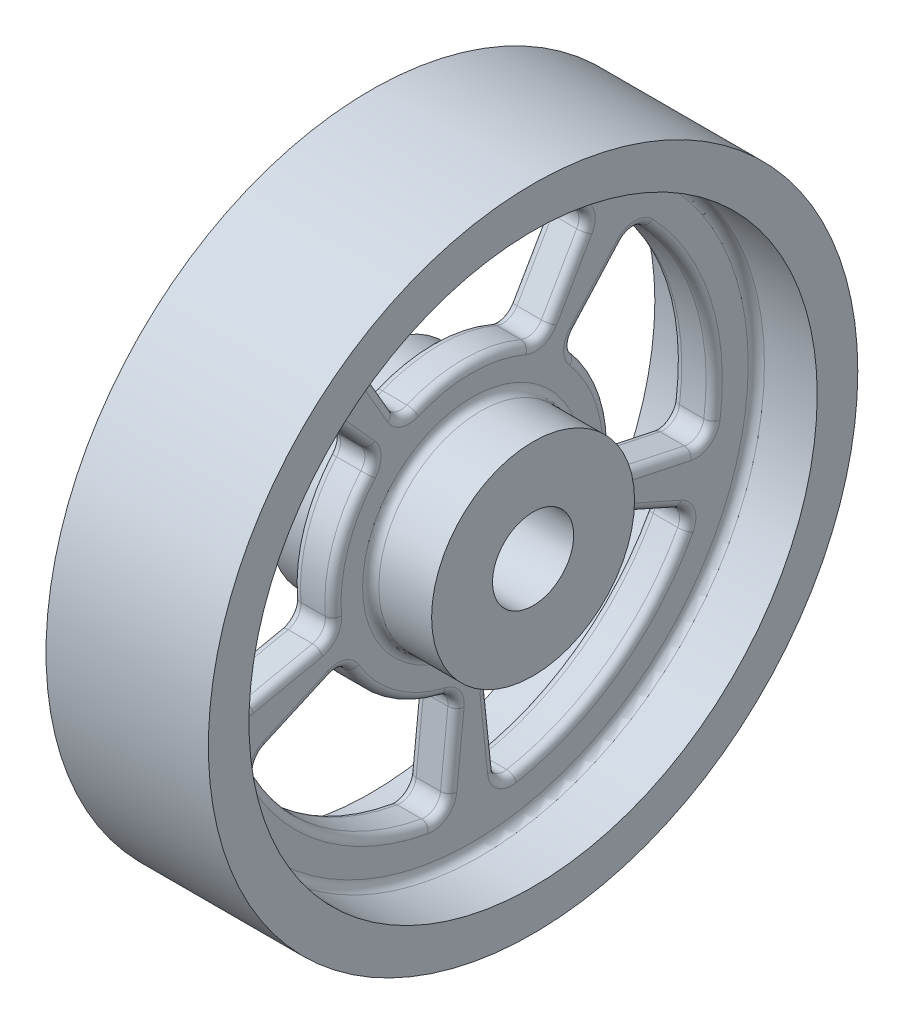
SolidWorks part; units mm, degrees
ref_plane "Front Plane" through (0, 0, 0) normal (0, 0, 1) x (1, 0, 0)
ref_plane "Top Plane" through (0, 0, 0) normal (0, 1, 0) x (1, 0, 0)
ref_plane "Right Plane" through (0, 0, 0) normal (1, 0, 0) x (0, 0, -1)
sketch "Sketch1" plane through (0, 0, 0) normal (0, 0, 1) x (1, 0, 0)
  line L0 (2.5, 12.5) -> (10, 12.5)
  line L9 (-10, 40) -> (10, 40)
  line L10 (-10, 40) -> (-10, 35)
  line L11 (-10, 35) -> (-2.5, 35)
  line L12 (10, 40) -> (10, 35)
  line L13 (0, 84.9625) -> (0, 0) construction
  line L14 (44.4387, 0) -> (0, 0) construction
  line L16 (-2.5, 35) -> (-2.5, 12.5)
  line L18 (2.5, 35) -> (2.5, 12.5)
  line L20 (10, 5) -> (-10, 5)
  line L21 (-10, 12.5) -> (-2.5, 12.5)
  line L22 (-10, 12.5) -> (-10, 5)
  line L24 (10, 12.5) -> (10, 5)
  line L25 (2.5, 35) -> (10, 35)
  point P0 (0, 71.5263)
  point P5 (0, 41.2843)
  point P10 (0, 22.1841)
  point P16 (0, 0)
  point P17 (0, 0)
  point P18 (68.2042, 76.8861)
  dimension "D1" = 20
  dimension "D2" = 5
  dimension "D3" = 5
  dimension "D4" = 80
  dimension "D5" = 25
  dimension "D6" = 10
revolve "Revolve2" add sketch "Sketch1" angle 360 about L14
sketch "Sketch3" plane through (-2.5, 0, 0) normal (-1, 0, 0) x (0, 0, 1)
  line L0 (0, 0) -> (0, 51.7683) construction
  line L5 (14.9224, 25.8464) -> (8.6212, 14.9323)
  line L6 (-14.9108, 25.8263) -> (-8.5859, 14.8711)
  arc A1 (8.6212, 14.9323) -> (-8.5859, 14.8711) centre (0.0739, -0.9089) ccw
  arc A2 (-14.9108, 25.8263) -> (14.9224, 25.8464) centre (0.0233, -0.1923) cw
  point P6 (8.6212, 14.8711)
  point P7 (14.9224, 25.8263)
  dimension "D1" = 30
  dimension "D2" = 18
  dimension "D3" = 60
extrude "Cut-Extrude1" cut sketch "Sketch3" against normal through all
fillet "Fillet1" radius 2 4 edges at (0, 25.8263, -14.9108) (0, 14.8711, -8.5859) (0, 14.9323, 8.6212) (0, 25.8464, 14.9224)
pattern_circular "CirPattern1" count 5 over 360 about axis through (0, 0, 0) along (1, 0, 0) of "Cut-Extrude1", "Fillet1"
fillet "Fillet2" radius 1 84 edges at (2.5, 15.6376, 8.4517) (2.5, 20.2891, 11.7139) (2.5, 25.6355, 14.0613) (2.5, 29.8076, 0.0016) (2.5, 25.6166, -14.0516) (2.5, 20.2552, -11.6943) (2.5, 15.5853, -8.4166) (2.5, -3.2058, 17.484) (2.5, -4.8709, 22.9159) (2.5, -5.4513, 28.726) (2.5, 9.2095, 28.3493) (2.5, 21.2798, 20.0206) (2.5, 17.3811, 15.6501) (2.5, 12.8208, 12.2216) (2.5, -17.6189, 2.354) (2.5, -23.2995, 2.4489) (2.5, -29.0046, 3.6923) (2.5, -24.1158, 17.5192) (2.5, -12.4649, 26.425) (2.5, -9.513, 21.3666) (2.5, -7.6616, 15.97) (2.5, -12.4745, -26.444) (2.5, -24.1139, -17.5218) (2.5, -28.9836, -3.689) (2.5, -23.2605, -2.4448) (2.5, -17.5559, -2.3516) (2.5, -13.8176, -10.0587) (2.5, -7.6833, -16.0292) (2.5, -3.1885, -17.4234) (2.5, 5.2965, -16.2496) (2.5, 12.8704, -12.2605) (2.5, 17.4103, -15.6763) (2.5, 21.2949, -20.0356) (2.5, 9.2126, -28.3483) (2.5, -5.4479, -28.705) (-2.5, 15.5853, -8.4166) (-2.5, 20.2552, -11.6943) (-2.5, 25.6166, -14.0516) (-2.5, 29.8076, 0.0016) (-2.5, 25.6355, 14.0613) (-2.5, 20.2891, 11.7139) (-2.5, 15.6376, 8.4517) (-2.5, 12.8208, 12.2216) (-2.5, 17.3811, 15.6501) (-2.5, 21.2798, 20.0206) (-2.5, 9.2095, 28.3493) (-2.5, -5.4513, 28.726) (-2.5, -4.8709, 22.9159) (-2.5, -3.2058, 17.484) (-2.5, -24.1158, 17.5192) (-2.5, -12.4649, 26.425) (-2.5, -9.513, 21.3666) (-2.5, -7.6616, 15.97) (-2.5, -13.8363, 10.033) (-2.5, -17.6189, 2.354) (-2.5, -23.2995, 2.4489) (-2.5, -12.4745, -26.444) (-2.5, -9.5289, -21.4024) (-2.5, -7.6833, -16.0292) (-2.5, -13.8176, -10.0587) (-2.5, -17.5559, -2.3516) (-2.5, -23.2605, -2.4448) (-2.5, -28.9836, -3.689) (-2.5, 21.2949, -20.0356) (-2.5, 17.4103, -15.6763) (-2.5, 12.8704, -12.2605) (-2.5, 5.2965, -16.2496) (-2.5, -3.1885, -17.4234) (-2.5, -4.8628, -22.8775) (-2.5, -5.4479, -28.705) (2.5, 0, -35) (2.5, 17.091, 0.0159) (2.5, 5.2663, 16.2594) (2.5, -13.8363, 10.033) (2.5, -9.5289, -21.4024) (2.5, -4.8628, -22.8775) (-2.5, 17.091, 0.0159) (-2.5, 5.2663, 16.2594) (-2.5, -29.0046, 3.6923) (-2.5, -24.1139, -17.5218) (-2.5, 9.2126, -28.3483) (-2.5, 0, -35) (2.5, 0, -12.5) (-2.5, 0, -12.5)
